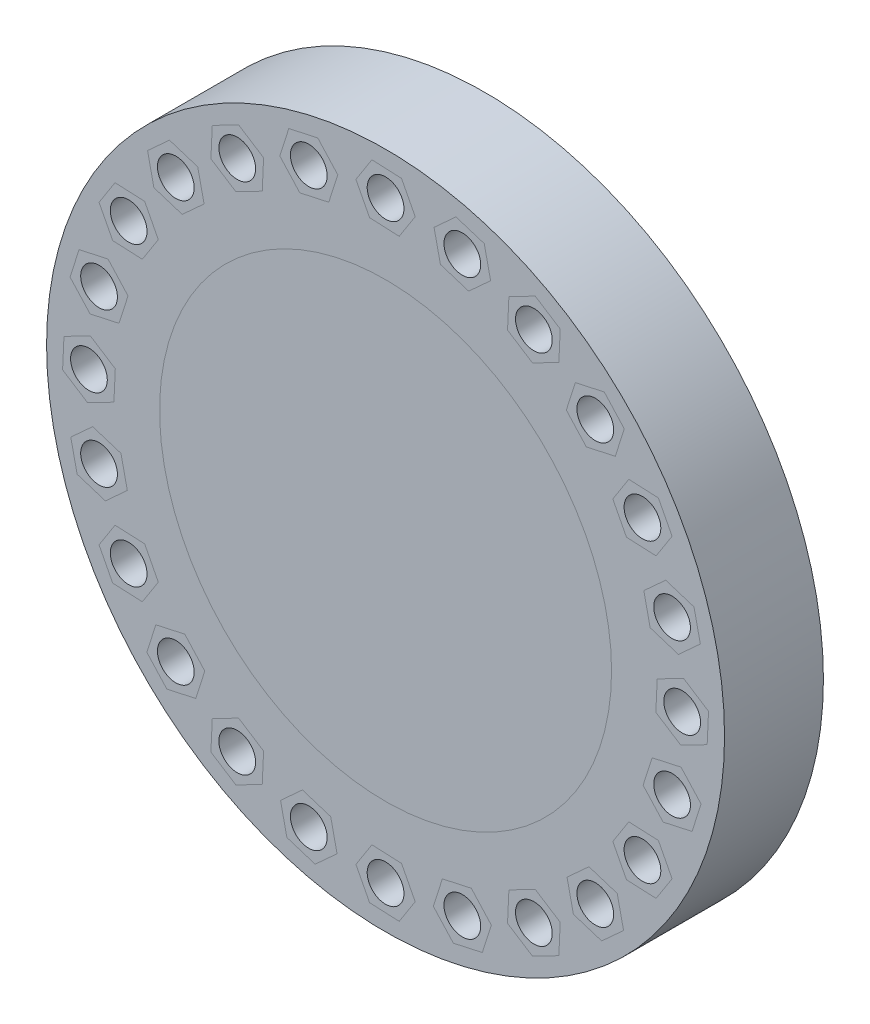
SolidWorks part; units mm, degrees
material "ASTM A36 Steel"
ref_plane "Front Plane" through (0, 0, 0) normal (0, 0, 1) x (1, 0, 0)
ref_plane "Top Plane" through (0, 0, 0) normal (0, 1, 0) x (1, 0, 0)
ref_plane "Right Plane" through (0, 0, 0) normal (1, 0, 0) x (0, 0, -1)
sketch "Sketch1" plane through (0, 0, 0) normal (0, 0, 1) x (1, 0, 0)
  circle A0 centre (0, 0) radius 304.8
  dimension "D1" = 609.6
extrude "Boss-Extrude1" add sketch "Sketch1" along normal blind 88.9
sketch "Sketch2" plane through (0, 0, 88.9) normal (0, 0, 1) x (1, 0, 0)
  circle A0 centre (0, 0) radius 266.7 construction
  circle A1 centre (0, 266.7) radius 16.51
  circle A2 centre (69.027, 257.6124) radius 16.51
  circle A3 centre (133.35, 230.969) radius 16.51
  circle A4 centre (188.5854, 188.5854) radius 16.51
  circle A5 centre (230.969, 133.35) radius 16.51
  circle A6 centre (257.6124, 69.027) radius 16.51
  circle A7 centre (266.7, 0) radius 16.51
  circle A8 centre (257.6124, -69.027) radius 16.51
  circle A9 centre (230.969, -133.35) radius 16.51
  circle A10 centre (188.5854, -188.5854) radius 16.51
  circle A11 centre (133.35, -230.969) radius 16.51
  circle A12 centre (69.027, -257.6124) radius 16.51
  circle A13 centre (0, -266.7) radius 16.51
  circle A14 centre (-69.027, -257.6124) radius 16.51
  circle A15 centre (-133.35, -230.969) radius 16.51
  circle A16 centre (-188.5854, -188.5854) radius 16.51
  circle A17 centre (-230.969, -133.35) radius 16.51
  circle A18 centre (-257.6124, -69.027) radius 16.51
  circle A19 centre (-266.7, 0) radius 16.51
  circle A20 centre (-257.6124, 69.027) radius 16.51
  circle A21 centre (-230.969, 133.35) radius 16.51
  circle A22 centre (-188.5854, 188.5854) radius 16.51
  circle A23 centre (-133.35, 230.969) radius 16.51
  circle A24 centre (-69.027, 257.6124) radius 16.51
  point P53 (0, 0)
  dimension "D1" = 24
extrude "Cut-Extrude6" cut sketch "Sketch2" against normal blind 88.9
sketch "Sketch5" plane through (0, 0, 88.9) normal (0, 0, 1) x (1, 0, 0)
  line L0 (49.3252, 239.6367) -> (74.7436, 231.5623)
  line L1 (-14.378, 244.2376) -> (12.264, 243.017)
  line L2 (12.264, 243.017) -> (26.6421, 265.4795)
  line L3 (26.6421, 265.4795) -> (14.378, 289.1624)
  line L4 (14.378, 289.1624) -> (-12.264, 290.383)
  line L5 (-12.264, 290.383) -> (-26.6421, 267.9205)
  line L6 (-26.6421, 267.9205) -> (-14.378, 244.2376)
  line L7 (74.7436, 231.5623) -> (94.4454, 249.538)
  line L8 (94.4454, 249.538) -> (88.7289, 275.5881)
  line L9 (88.7289, 275.5881) -> (63.3105, 283.6626)
  line L10 (63.3105, 283.6626) -> (43.6087, 265.6868)
  line L11 (43.6087, 265.6868) -> (49.3252, 239.6367)
  line L12 (109.667, 218.705) -> (132.1295, 204.3269)
  line L13 (132.1295, 204.3269) -> (155.8124, 216.5909)
  line L14 (155.8124, 216.5909) -> (157.033, 243.233)
  line L15 (157.033, 243.233) -> (134.5705, 257.611)
  line L16 (134.5705, 257.611) -> (110.8876, 245.347)
  line L17 (110.8876, 245.347) -> (109.667, 218.705)
  line L18 (162.5352, 182.8689) -> (180.511, 163.167)
  line L19 (180.511, 163.167) -> (206.5611, 168.8836)
  line L20 (206.5611, 168.8836) -> (214.6355, 194.3019)
  line L21 (214.6355, 194.3019) -> (196.6598, 214.0037)
  line L22 (196.6598, 214.0037) -> (170.6096, 208.2872)
  line L23 (170.6096, 208.2872) -> (162.5352, 182.8689)
  line L24 (204.3269, 134.5705) -> (216.5909, 110.8876)
  line L25 (216.5909, 110.8876) -> (243.233, 109.667)
  line L26 (243.233, 109.667) -> (257.611, 132.1295)
  line L27 (257.611, 132.1295) -> (245.347, 155.8124)
  line L28 (245.347, 155.8124) -> (218.705, 157.033)
  line L29 (218.705, 157.033) -> (204.3269, 134.5705)
  line L30 (232.1941, 77.1015) -> (237.9106, 51.0513)
  line L31 (237.9106, 51.0513) -> (263.3289, 42.9769)
  line L32 (263.3289, 42.9769) -> (283.0308, 60.9526)
  line L33 (283.0308, 60.9526) -> (277.3142, 87.0028)
  line L34 (277.3142, 87.0028) -> (251.8959, 95.0772)
  line L35 (251.8959, 95.0772) -> (232.1941, 77.1015)
  line L36 (244.2376, 14.378) -> (243.017, -12.264)
  line L37 (243.017, -12.264) -> (265.4795, -26.6421)
  line L38 (265.4795, -26.6421) -> (289.1624, -14.378)
  line L39 (289.1624, -14.378) -> (290.383, 12.264)
  line L40 (290.383, 12.264) -> (267.9205, 26.6421)
  line L41 (267.9205, 26.6421) -> (244.2376, 14.378)
  line L42 (239.6367, -49.3252) -> (231.5623, -74.7436)
  line L43 (231.5623, -74.7436) -> (249.538, -94.4454)
  line L44 (249.538, -94.4454) -> (275.5881, -88.7289)
  line L45 (275.5881, -88.7289) -> (283.6626, -63.3105)
  line L46 (283.6626, -63.3105) -> (265.6868, -43.6087)
  line L47 (265.6868, -43.6087) -> (239.6367, -49.3252)
  line L48 (218.705, -109.667) -> (204.3269, -132.1295)
  line L49 (204.3269, -132.1295) -> (216.5909, -155.8124)
  line L50 (216.5909, -155.8124) -> (243.233, -157.033)
  line L51 (243.233, -157.033) -> (257.611, -134.5705)
  line L52 (257.611, -134.5705) -> (245.347, -110.8876)
  line L53 (245.347, -110.8876) -> (218.705, -109.667)
  line L54 (182.8689, -162.5352) -> (163.167, -180.511)
  line L55 (163.167, -180.511) -> (168.8836, -206.5611)
  line L56 (168.8836, -206.5611) -> (194.3019, -214.6355)
  line L57 (194.3019, -214.6355) -> (214.0037, -196.6598)
  line L58 (214.0037, -196.6598) -> (208.2872, -170.6096)
  line L59 (208.2872, -170.6096) -> (182.8689, -162.5352)
  line L60 (134.5705, -204.3269) -> (110.8876, -216.5909)
  line L61 (110.8876, -216.5909) -> (109.667, -243.233)
  line L62 (109.667, -243.233) -> (132.1295, -257.611)
  line L63 (132.1295, -257.611) -> (155.8124, -245.347)
  line L64 (155.8124, -245.347) -> (157.033, -218.705)
  line L65 (157.033, -218.705) -> (134.5705, -204.3269)
  line L66 (77.1015, -232.1941) -> (51.0513, -237.9106)
  line L67 (51.0513, -237.9106) -> (42.9769, -263.3289)
  line L68 (42.9769, -263.3289) -> (60.9526, -283.0308)
  line L69 (60.9526, -283.0308) -> (87.0028, -277.3142)
  line L70 (87.0028, -277.3142) -> (95.0772, -251.8959)
  line L71 (95.0772, -251.8959) -> (77.1015, -232.1941)
  line L72 (14.378, -244.2376) -> (-12.264, -243.017)
  line L73 (-12.264, -243.017) -> (-26.6421, -265.4795)
  line L74 (-26.6421, -265.4795) -> (-14.378, -289.1624)
  line L75 (-14.378, -289.1624) -> (12.264, -290.383)
  line L76 (12.264, -290.383) -> (26.6421, -267.9205)
  line L77 (26.6421, -267.9205) -> (14.378, -244.2376)
  line L78 (-49.3252, -239.6367) -> (-74.7436, -231.5623)
  line L79 (-74.7436, -231.5623) -> (-94.4454, -249.538)
  line L80 (-94.4454, -249.538) -> (-88.7289, -275.5881)
  line L81 (-88.7289, -275.5881) -> (-63.3105, -283.6626)
  line L82 (-63.3105, -283.6626) -> (-43.6087, -265.6868)
  line L83 (-43.6087, -265.6868) -> (-49.3252, -239.6367)
  line L84 (-109.667, -218.705) -> (-132.1295, -204.3269)
  line L85 (-132.1295, -204.3269) -> (-155.8124, -216.5909)
  line L86 (-155.8124, -216.5909) -> (-157.033, -243.233)
  line L87 (-157.033, -243.233) -> (-134.5705, -257.611)
  line L88 (-134.5705, -257.611) -> (-110.8876, -245.347)
  line L89 (-110.8876, -245.347) -> (-109.667, -218.705)
  line L90 (-162.5352, -182.8689) -> (-180.511, -163.167)
  line L91 (-180.511, -163.167) -> (-206.5611, -168.8836)
  line L92 (-206.5611, -168.8836) -> (-214.6355, -194.3019)
  line L93 (-214.6355, -194.3019) -> (-196.6598, -214.0037)
  line L94 (-196.6598, -214.0037) -> (-170.6096, -208.2872)
  line L95 (-170.6096, -208.2872) -> (-162.5352, -182.8689)
  line L96 (-204.3269, -134.5705) -> (-216.5909, -110.8876)
  line L97 (-216.5909, -110.8876) -> (-243.233, -109.667)
  line L98 (-243.233, -109.667) -> (-257.611, -132.1295)
  line L99 (-257.611, -132.1295) -> (-245.347, -155.8124)
  line L100 (-245.347, -155.8124) -> (-218.705, -157.033)
  line L101 (-218.705, -157.033) -> (-204.3269, -134.5705)
  line L102 (-232.1941, -77.1015) -> (-237.9106, -51.0513)
  line L103 (-237.9106, -51.0513) -> (-263.3289, -42.9769)
  line L104 (-263.3289, -42.9769) -> (-283.0308, -60.9526)
  line L105 (-283.0308, -60.9526) -> (-277.3142, -87.0028)
  line L106 (-277.3142, -87.0028) -> (-251.8959, -95.0772)
  line L107 (-251.8959, -95.0772) -> (-232.1941, -77.1015)
  line L108 (-244.2376, -14.378) -> (-243.017, 12.264)
  line L109 (-243.017, 12.264) -> (-265.4795, 26.6421)
  line L110 (-265.4795, 26.6421) -> (-289.1624, 14.378)
  line L111 (-289.1624, 14.378) -> (-290.383, -12.264)
  line L112 (-290.383, -12.264) -> (-267.9205, -26.6421)
  line L113 (-267.9205, -26.6421) -> (-244.2376, -14.378)
  line L114 (-239.6367, 49.3252) -> (-231.5623, 74.7436)
  line L115 (-231.5623, 74.7436) -> (-249.538, 94.4454)
  line L116 (-249.538, 94.4454) -> (-275.5881, 88.7289)
  line L117 (-275.5881, 88.7289) -> (-283.6626, 63.3105)
  line L118 (-283.6626, 63.3105) -> (-265.6868, 43.6087)
  line L119 (-265.6868, 43.6087) -> (-239.6367, 49.3252)
  line L120 (-218.705, 109.667) -> (-204.3269, 132.1295)
  line L121 (-204.3269, 132.1295) -> (-216.5909, 155.8124)
  line L122 (-216.5909, 155.8124) -> (-243.233, 157.033)
  line L123 (-243.233, 157.033) -> (-257.611, 134.5705)
  line L124 (-257.611, 134.5705) -> (-245.347, 110.8876)
  line L125 (-245.347, 110.8876) -> (-218.705, 109.667)
  line L126 (-182.8689, 162.5352) -> (-163.167, 180.511)
  line L127 (-163.167, 180.511) -> (-168.8836, 206.5611)
  line L128 (-168.8836, 206.5611) -> (-194.3019, 214.6355)
  line L129 (-194.3019, 214.6355) -> (-214.0037, 196.6598)
  line L130 (-214.0037, 196.6598) -> (-208.2872, 170.6096)
  line L131 (-208.2872, 170.6096) -> (-182.8689, 162.5352)
  line L132 (-134.5705, 204.3269) -> (-110.8876, 216.5909)
  line L133 (-110.8876, 216.5909) -> (-109.667, 243.233)
  line L134 (-109.667, 243.233) -> (-132.1295, 257.611)
  line L135 (-132.1295, 257.611) -> (-155.8124, 245.347)
  line L136 (-155.8124, 245.347) -> (-157.033, 218.705)
  line L137 (-157.033, 218.705) -> (-134.5705, 204.3269)
  line L138 (-77.1015, 232.1941) -> (-51.0513, 237.9106)
  line L139 (-51.0513, 237.9106) -> (-42.9769, 263.3289)
  line L140 (-42.9769, 263.3289) -> (-60.9526, 283.0308)
  line L141 (-60.9526, 283.0308) -> (-87.0028, 277.3142)
  line L142 (-87.0028, 277.3142) -> (-95.0772, 251.8959)
  line L143 (-95.0772, 251.8959) -> (-77.1015, 232.1941)
  circle A0 centre (0, 0) radius 203.2
  circle A1 centre (0, 266.7) radius 23.0969 construction
  point P153 (0, 0)
  dimension "D1" = 26.67
  dimension "D3" = 406.4
  dimension "D2" = 24
split line "Split Line2"
